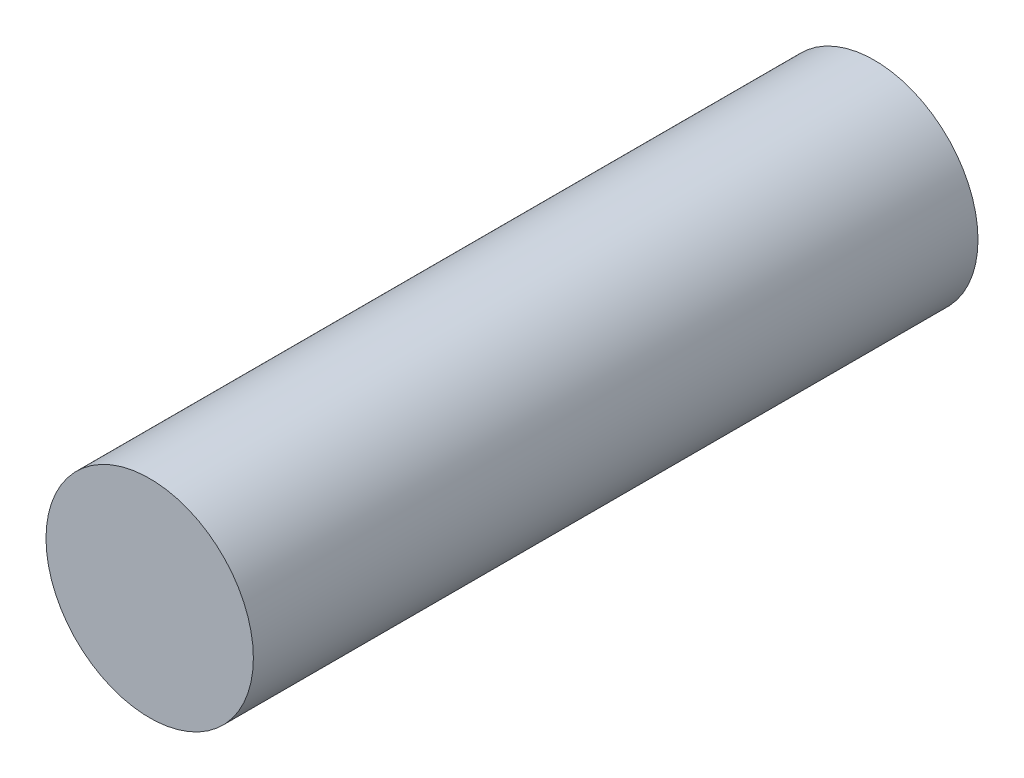
SolidWorks part; units mm, degrees
ref_plane "Спереди" through (0, 0, 0) normal (0, 0, 1) x (1, 0, 0)
ref_plane "Сверху" through (0, 0, 0) normal (0, 1, 0) x (1, 0, 0)
ref_plane "Справа" through (0, 0, 0) normal (1, 0, 0) x (0, 0, -1)
sketch "Sketch1" plane through (0, 0, 0) normal (0, 0, 1) x (1, 0, 0)
  circle A0 centre (0, 0) radius 9.3
  dimension "D1" = 18.6
extrude "Boss-Extrude1" add sketch "Sketch1" along normal blind 65
